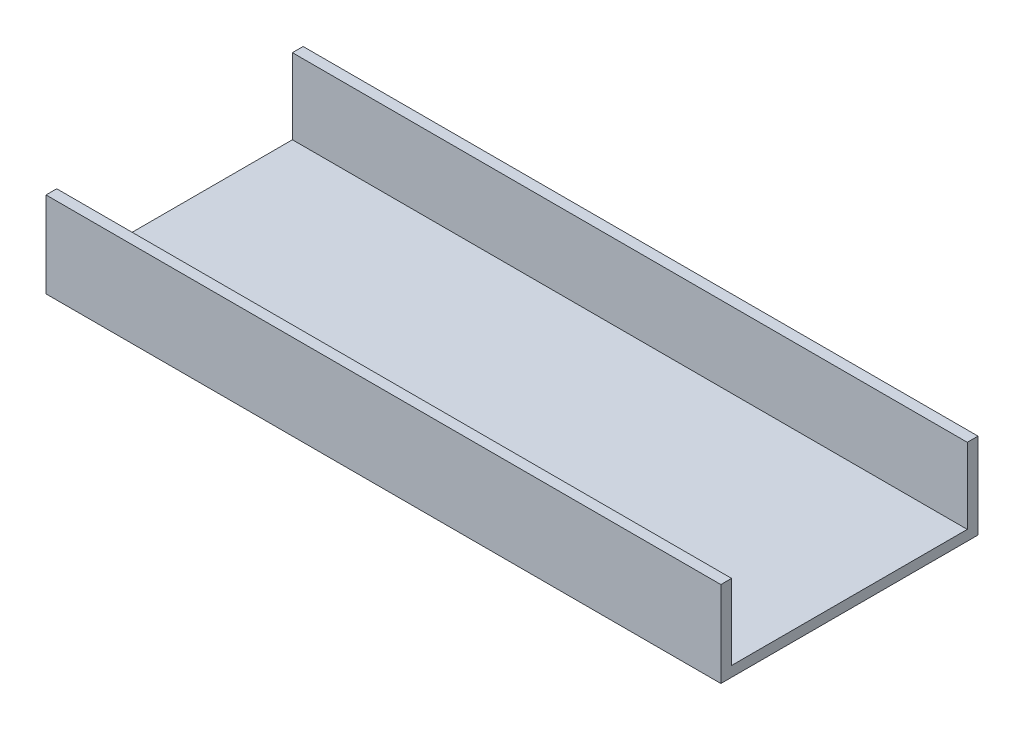
SolidWorks part; units mm, degrees
ref_plane "Front Plane" through (0, 0, 0) normal (0, 0, 1) x (1, 0, 0)
ref_plane "Top Plane" through (0, 0, 0) normal (0, 1, 0) x (1, 0, 0)
ref_plane "Right Plane" through (0, 0, 0) normal (1, 0, 0) x (0, 0, -1)
sketch "Sketch1" plane through (0, 0, 0) normal (1, 0, 0) x (0, 0, -1)
  line L0 (48.7481, 22.352) -> (48.7481, 0)
  line L1 (48.7481, 0) -> (-21.1019, 0)
  line L2 (-21.1019, 0) -> (-21.1019, 22.352)
  line L3 (48.7481, 22.352) -> (51.9231, 22.352)
  line L4 (51.9231, 22.352) -> (51.9231, -3.048)
  line L5 (51.9231, -3.048) -> (-24.2769, -3.048)
  line L6 (-24.2769, -3.048) -> (-24.2769, 22.352)
  line L7 (-24.2769, 22.352) -> (-21.1019, 22.352)
  dimension "D1" = 3.175
  dimension "D2" = 69.85
  dimension "D3" = 25.4
  dimension "D4" = 22.352
extrude "Boss-Extrude1" add sketch "Sketch1" along normal blind 200
